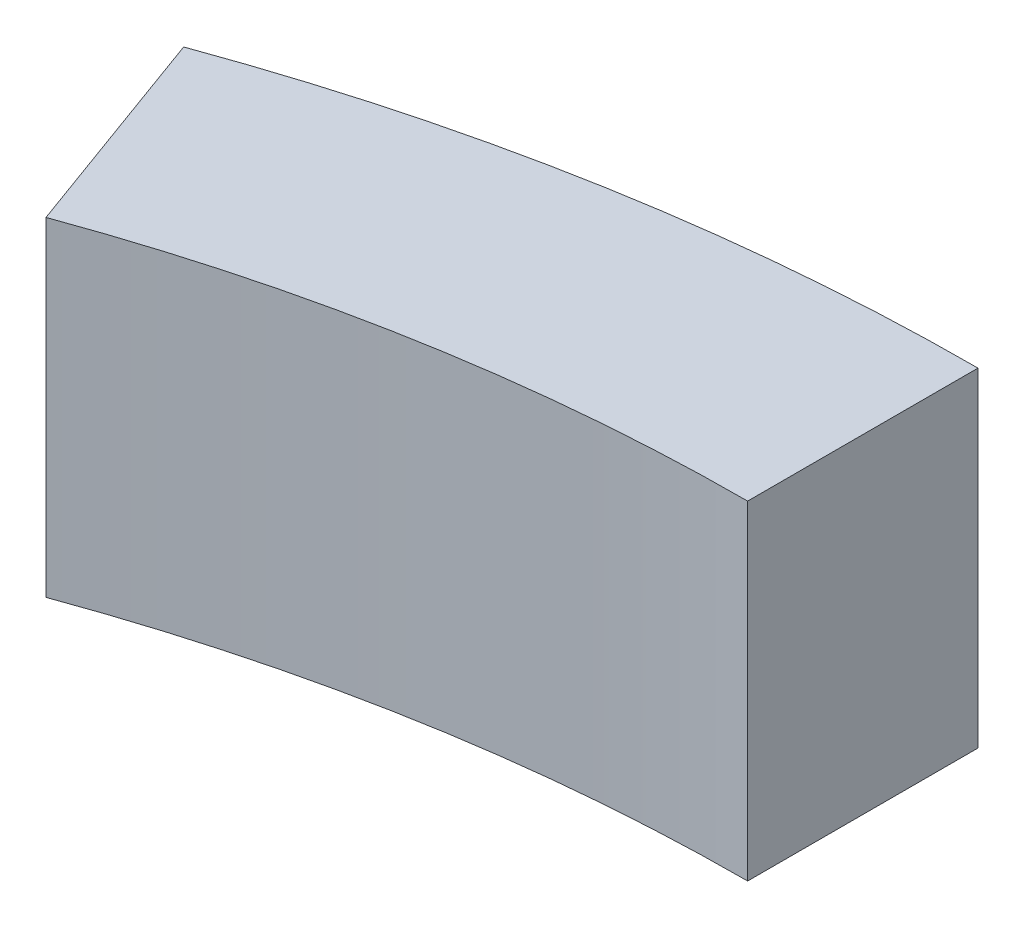
SolidWorks part; units mm, degrees
ref_plane "Ebene vorne" through (0, 0, 0) normal (0, 0, 1) x (1, 0, 0)
ref_plane "Ebene oben" through (0, 0, 0) normal (0, 1, 0) x (1, 0, 0)
ref_plane "Ebene rechts" through (0, 0, 0) normal (1, 0, 0) x (0, 0, -1)
sketch "Skizze1" plane through (0, 0, 0) normal (0, 1, 0) x (1, 0, 0)
  line L0 (-20.5212, 56.3816) -> (-18.1271, 49.8037)
  line L1 (0, 53) -> (0, 60)
  arc A0 (-20.5212, 56.3816) -> (0, 60) centre (0, 0) cw
  arc A1 (-18.1271, 49.8037) -> (0, 53) centre (0, 0) cw
  dimension "D1" = 60
  dimension "D3" = 53
  dimension "D2" = 20
extrude "Aufsatz-Linear austragen1" add sketch "Skizze1" along normal blind 10
